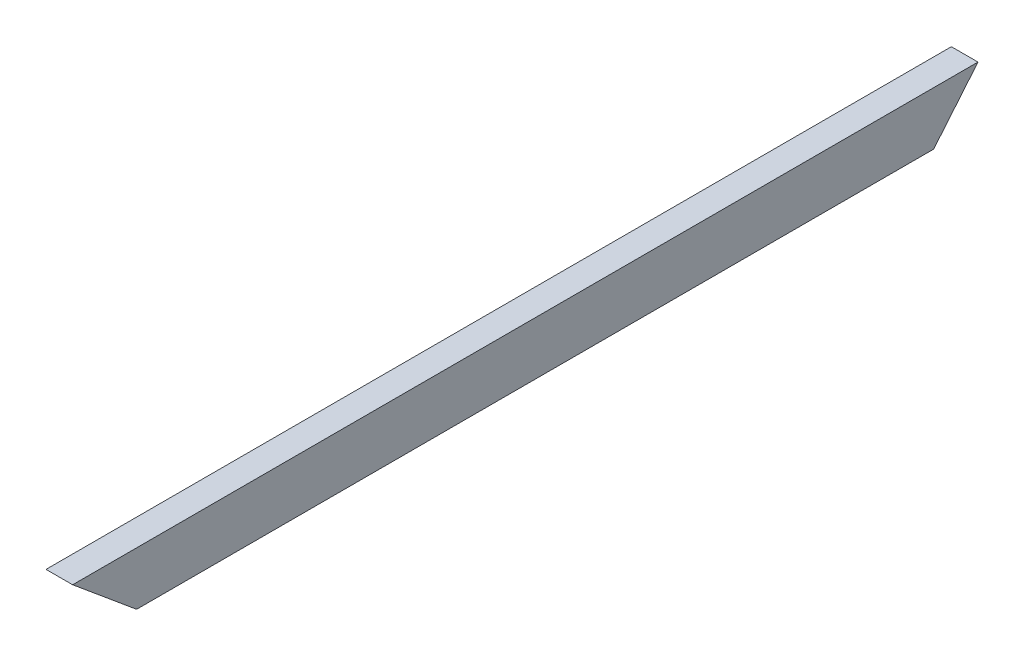
SolidWorks part; units mm, degrees
material "6063-T6"
ref_plane "Front" through (0, 0, 0) normal (0, 0, 1) x (1, 0, 0)
ref_plane "Top" through (0, 0, 0) normal (0, 1, 0) x (1, 0, 0)
ref_plane "Right" through (0, 0, 0) normal (1, 0, 0) x (0, 0, -1)
sketch "Sketch1" plane through (0, 0, 0) normal (0, 0, 1) x (1, 0, 0)
  line L0 (3.175, 3.175) -> (3.175, 22.225)
  line L1 (0, 0) -> (12.7, 0)
  line L2 (0, 0) -> (0, 25.4)
  line L3 (0, 25.4) -> (12.7, 25.4)
  line L4 (12.7, 0) -> (12.7, 25.4)
  line L5 (0, 0) -> (12.7, 25.4) construction
  line L6 (0, 25.4) -> (12.7, 0) construction
  line L7 (3.175, 22.225) -> (9.525, 22.225)
  line L8 (9.525, 3.175) -> (9.525, 22.225)
  line L9 (3.175, 3.175) -> (9.525, 3.175)
  point P4 (6.35, 12.7)
  dimension "D1" = 25.4
  dimension "D2" = 12.7
  dimension "D3" = 3.175
extrude "Boss-Extrude1" add sketch "Sketch1" along normal blind 431.8
sketch "Sketch2" plane through (12.7, 0, 0) normal (1, 0, 0) x (0, 0, -1)
  line L1 (-471.9693, 58.8252) -> (-179.1006, -184.8733) construction
  line L2 (-431.8, 25.4) -> (-401.2751, 0)
  line L3 (-431.8, 25.4) -> (-431.8, 0)
  line L4 (-431.8, 0) -> (-401.2751, 0)
  line L5 (-431.8, 0) -> (0, 0) construction
extrude "Cut-Extrude1" cut sketch "Sketch2" against normal through all
sketch "Sketch3" plane through (12.7, 0, 0) normal (1, 0, 0) x (0, 0, -1)
  line L0 (-180.7217, -191.7853) -> (38.6069, 71.7965) construction
  line L1 (-21.1356, 0) -> (0, 25.4)
  line L2 (0, 25.4) -> (0, 0)
  line L3 (0, 0) -> (-21.1356, 0)
  line L4 (-401.2751, 0) -> (0, 0) construction
extrude "Cut-Extrude2" cut sketch "Sketch3" against normal through all
